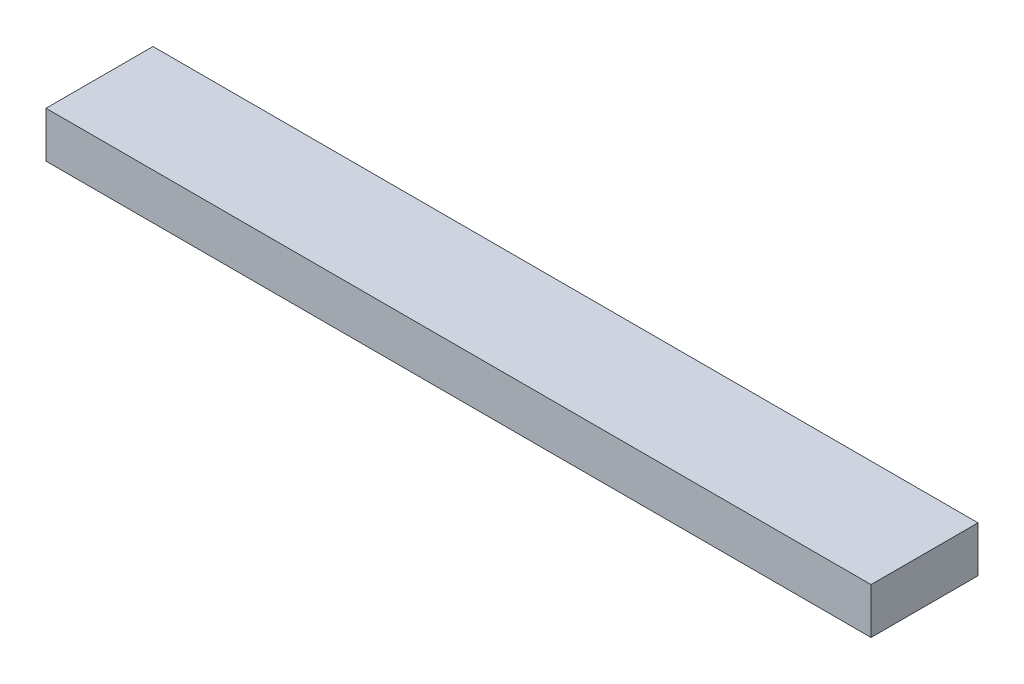
SolidWorks part; units mm, degrees
material "Pine"
ref_plane "Front Plane" through (0, 0, 0) normal (0, 0, 1) x (1, 0, 0)
ref_plane "Top Plane" through (0, 0, 0) normal (0, 1, 0) x (1, 0, 0)
ref_plane "Right Plane" through (0, 0, 0) normal (1, 0, 0) x (0, 0, -1)
sketch "Sketch1" plane through (0, 0, 0) normal (0, 1, 0) x (1, 0, 0)
  line L1 (0, 0) -> (685.8, 0)
  line L2 (0, 0) -> (0, 88.9)
  line L3 (0, 88.9) -> (685.8, 88.9)
  line L4 (685.8, 0) -> (685.8, 88.9)
  dimension "D1" = 88.9
  dimension "D2" = 685.8
extrude "Boss-Extrude1" add sketch "Sketch1" along normal blind 38.1
